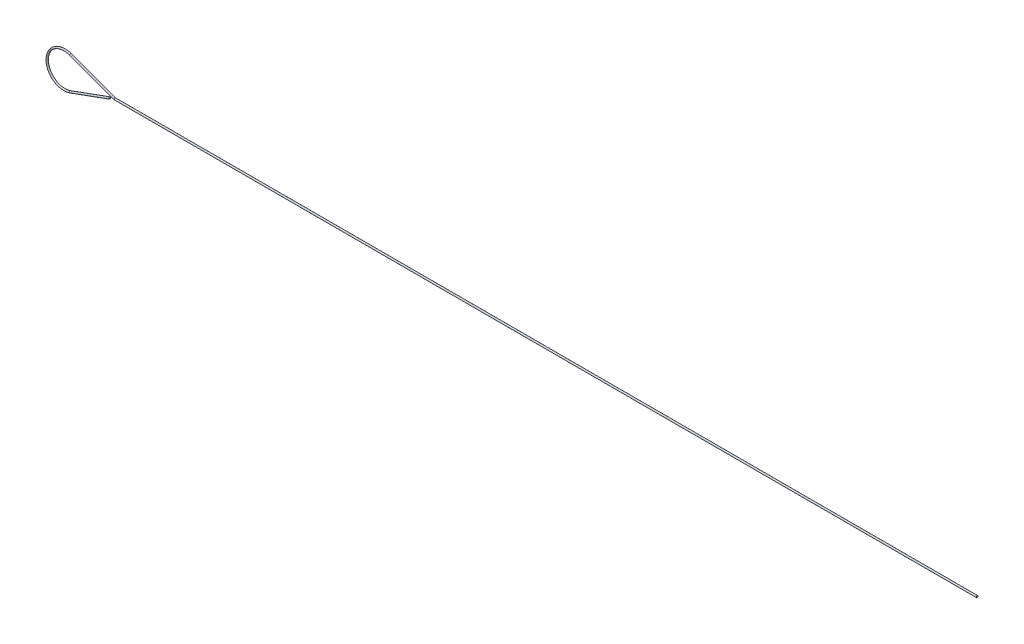
SolidWorks part; units mm, degrees
ref_plane "Plan de face" through (0, 0, 0) normal (0, 0, 1) x (1, 0, 0)
ref_plane "Plan de dessus" through (0, 0, 0) normal (0, 1, 0) x (1, 0, 0)
ref_plane "Plan de droite" through (0, 0, 0) normal (1, 0, 0) x (0, 0, -1)
sketch "Esquisse1" plane through (0, 0, 0) normal (0, 0, 1) x (1, 0, 0)
  line L0 (29.238, 0) -> (529.238, 0)
  line L1 (29.238, 0) -> (3.4202, 9.3969)
  line L2 (26.341, -1.0544) -> (3.4202, -9.3969)
  arc A0 (3.4202, 9.3969) -> (3.4202, -9.3969) centre (0, 0) ccw
  dimension "D1" = 20
  dimension "D2" = 160
  dimension "D3" = 160
  dimension "D5" = 500
ref_plane "Plan1" through (529.238, 0, 0) normal (1, 0, 0) x (0, 0, -1)
sketch "Esquisse3" plane through (529.238, 0, 0) normal (1, 0, 0) x (0, 0, -1)
  circle A0 centre (0, 0) radius 0.5
  dimension "D1" = 1
sweep "Balayage2" add profiles "Esquisse3" path "Esquisse1"
